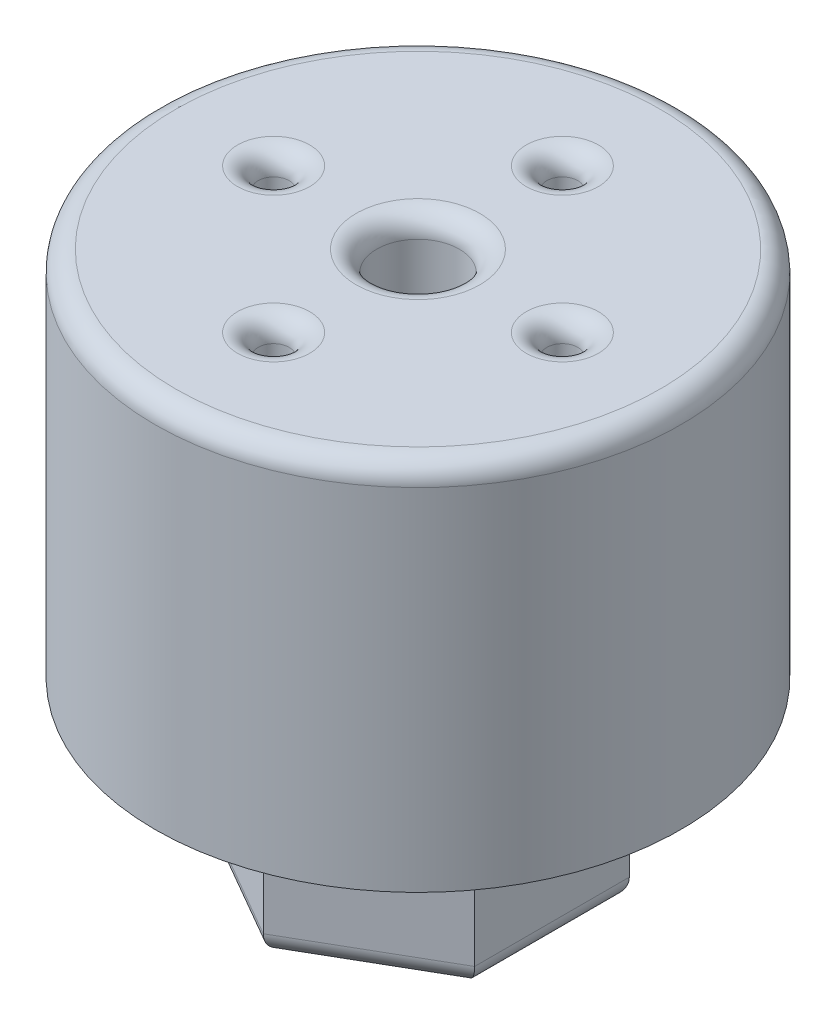
SolidWorks part; units mm, degrees
ref_plane "Alzado" through (0, 0, 0) normal (0, 0, 1) x (1, 0, 0)
ref_plane "Planta" through (0, 0, 0) normal (0, 1, 0) x (1, 0, 0)
ref_plane "Vista lateral" through (0, 0, 0) normal (1, 0, 0) x (0, 0, -1)
sketch "Croquis1" plane through (0, 0, 0) normal (0, 1, 0) x (1, 0, 0)
  line L0 (0, 0) -> (0, 12.75) construction
  circle A0 centre (0, 0) radius 12.75
  circle A1 centre (0, 7) radius 0.75
  circle A2 centre (7, 0) radius 0.75
  circle A3 centre (0, -7) radius 0.75
  circle A4 centre (-7, 0) radius 0.75
  point P15 (0, 0)
  dimension "D1" = 25.5
  dimension "D3" = 1.5
  dimension "D2" = 7
  dimension "D4" = 4
extrude "Saliente-Extruir1" add sketch "Croquis1" along normal blind 18
sketch "Croquis3" plane through (0, 0, 0) normal (0, -1, 0) x (1, 0, 0)
  line L1 (0, 7.5) -> (-6.4952, 3.75)
  line L2 (-6.4952, 3.75) -> (-6.4952, -3.75)
  line L3 (-6.4952, -3.75) -> (0, -7.5)
  line L4 (0, -7.5) -> (6.4952, -3.75)
  line L5 (6.4952, -3.75) -> (6.4952, 3.75)
  line L6 (6.4952, 3.75) -> (0, 7.5)
  circle A0 centre (0, 0) radius 7.5 construction
extrude "Saliente-Extruir3" add sketch "Croquis3" along normal blind 8
sketch "Croquis4" plane through (0, 0, 0) normal (0, -1, 0) x (1, 0, 0)
  circle A0 centre (0, 0) radius 12.75
extrude "Saliente-Extruir4" add sketch "Croquis4" against normal blind 4
sketch "Croquis5" plane through (0, -8, 0) normal (0, -1, 0) x (1, 0, 0)
  circle A0 centre (0, 0) radius 2
  dimension "D1" = 4
extrude "Cortar-Extruir1" cut sketch "Croquis5" against normal through all
fillet "Redondeo1" radius 1 7 edges at (6.4952, -8, 0) (3.2476, -8, -5.625) (-3.2476, -8, -5.625) (-6.4952, -8, 0) (-3.2476, -8, 5.625) (3.2476, -8, 5.625) (0, -8, -2)
fillet "Redondeo2" radius 1 6 edges at (-7, 18, 0.75) (7, 18, 0.75) (0, 18, 12.75) (0, 18, -6.25) (0, 18, 7.75) (0, 18, -2)
